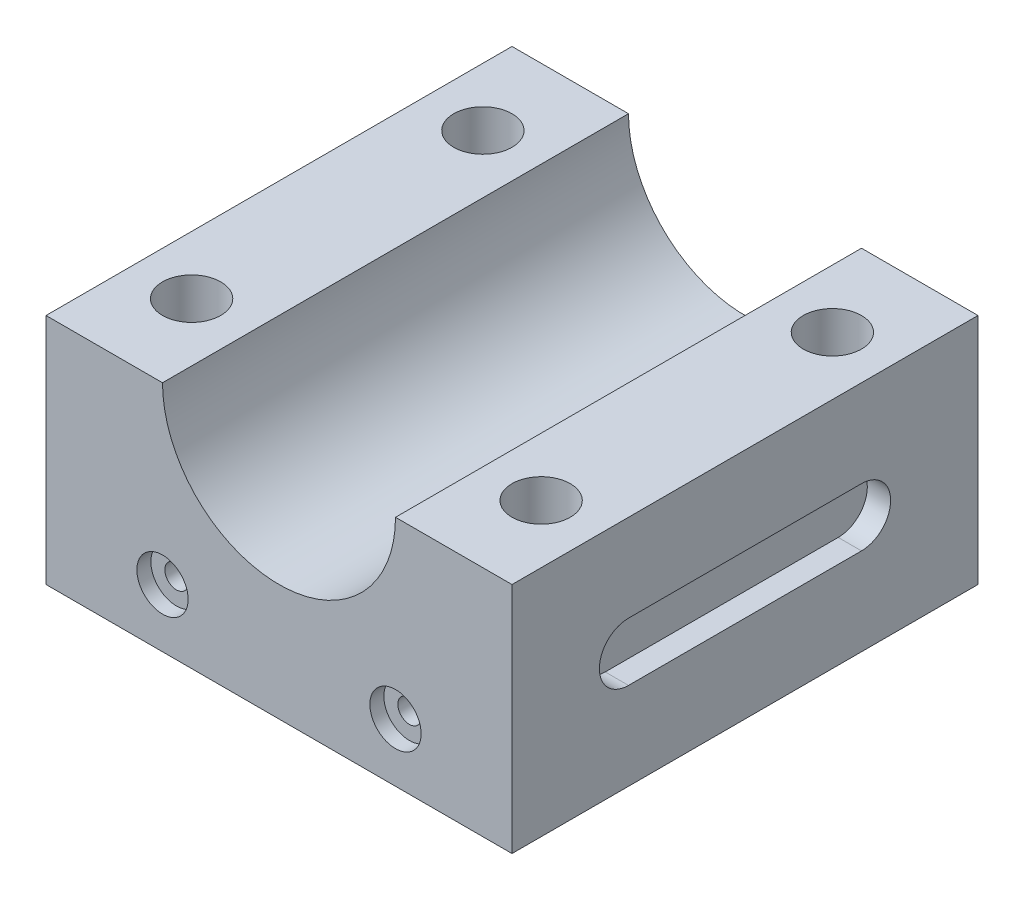
SolidWorks part; units mm, degrees
ref_plane "Front Plane" through (0, 0, 0) normal (0, 0, 1) x (1, 0, 0)
ref_plane "Top Plane" through (0, 0, 0) normal (0, 1, 0) x (1, 0, 0)
ref_plane "Right Plane" through (0, 0, 0) normal (1, 0, 0) x (0, 0, -1)
sketch "Sketch1" plane through (0, 0, 0) normal (0, 0, 1) x (1, 0, 0)
  line L0 (25.4, 25.4) -> (50.8, 25.4)
  line L1 (-50.8, -25.4) -> (50.8, -25.4)
  line L2 (-50.8, -25.4) -> (-50.8, 25.4)
  line L3 (-50.8, 25.4) -> (-25.4, 25.4)
  line L4 (50.8, -25.4) -> (50.8, 25.4)
  line L5 (-50.8, -25.4) -> (50.8, 25.4) construction
  line L6 (-50.8, 25.4) -> (50.8, -25.4) construction
  arc A0 (-25.4, 25.4) -> (25.4, 25.4) centre (0, 25.4) ccw
  point P0 (0, 0)
  point P9 (0, 0)
  point P10 (-26.4821, 25.4)
  point P11 (-33.1026, 25.4)
  point P12 (-1.4558, 25.4)
  point P13 (0, 0)
  dimension "D1" = 101.6
  dimension "D2" = 50.8
extrude "Boss-Extrude1" add sketch "Sketch1" along normal mid plane 101.6
sketch "Sketch2" plane through (0, 25.4, 0) normal (0, 1, 0) x (1, 0, 0)
  line L0 (-25.4, 50.8) -> (-50.8, 50.8) construction
  circle A0 centre (-38.1, 31.75) radius 6.35
  point P0 (-38.1, 31.75)
  point P5 (-38.1, 50.8)
  point P6 (-38.1, 31.75)
  dimension "D2" = 12.7
  dimension "D1" = 19.05
extrude "Cut-Extrude1" cut sketch "Sketch2" against normal through all contours A0
pattern_linear "LPattern1" count 2 spacing 76.2 along (1, 0, 0) count 2 spacing 63.5 along (0, 0, 1) of "Cut-Extrude1"
sketch "Sketch5" plane through (0, 0, 50.8) normal (0, 0, 1) x (1, 0, 0)
  line L0 (-50.8, 25.4) -> (-50.8, -25.4) construction
  line L1 (-50.8, -25.4) -> (50.8, -25.4) construction
  line L2 (0, -27.94) -> (0, 27.94) construction
  point P0 (-25.4, -12.7)
  point P8 (25.4, -12.7)
  dimension "D1" = 25.4
  dimension "D2" = 12.7
hole_wizard "CBORE for #00 Binding Head Machine Screw1" positions "Sketch5" profile "Sketch6" counterbore size "#00" standard "ANSI Inch" end condition through all
sketch "Sketch6" plane through (-25.4, -12.7, 50.8) normal (1, 0, 0) x (0, -1, 0)
  line L0 (0, 0) -> (0, 101.6)
  line L1 (0, 101.6) -> (2.54, 101.6)
  line L3 (2.54, 101.6) -> (2.54, 3.048)
  line L4 (2.54, 3.048) -> (5.588, 3.048)
  line L5 (5.588, 3.048) -> (5.588, 0)
  line L7 (5.588, 0) -> (0, 0)
  line L11 (0, -6.35) -> (0, 107.95) construction
  dimension "Thru Hole Dia." = 5.08
  dimension "Thru Hole Depth" = 101.6
  dimension "C'Bore Dia." = 11.176
  dimension "C'Bore Depth" = 3.048
sketch "Sketch7" plane through (50.8, 0, 0) normal (1, 0, 0) x (0, 0, -1)
  line L0 (-25.4, 0) -> (25.4, 0) construction
  line L1 (-25.4, 6.35) -> (25.4, 6.35)
  line L2 (-25.4, -6.35) -> (25.4, -6.35)
  arc A0 (-25.4, 6.35) -> (-25.4, -6.35) centre (-25.4, 0) ccw
  arc A1 (25.4, -6.35) -> (25.4, 6.35) centre (25.4, 0) ccw
  point P2 (0, 0)
  point P7 (0, 0)
  dimension "D2" = 6.35
  dimension "D1" = 50.8
extrude "Cut-Extrude6" cut sketch "Sketch7" against normal blind 5.08
